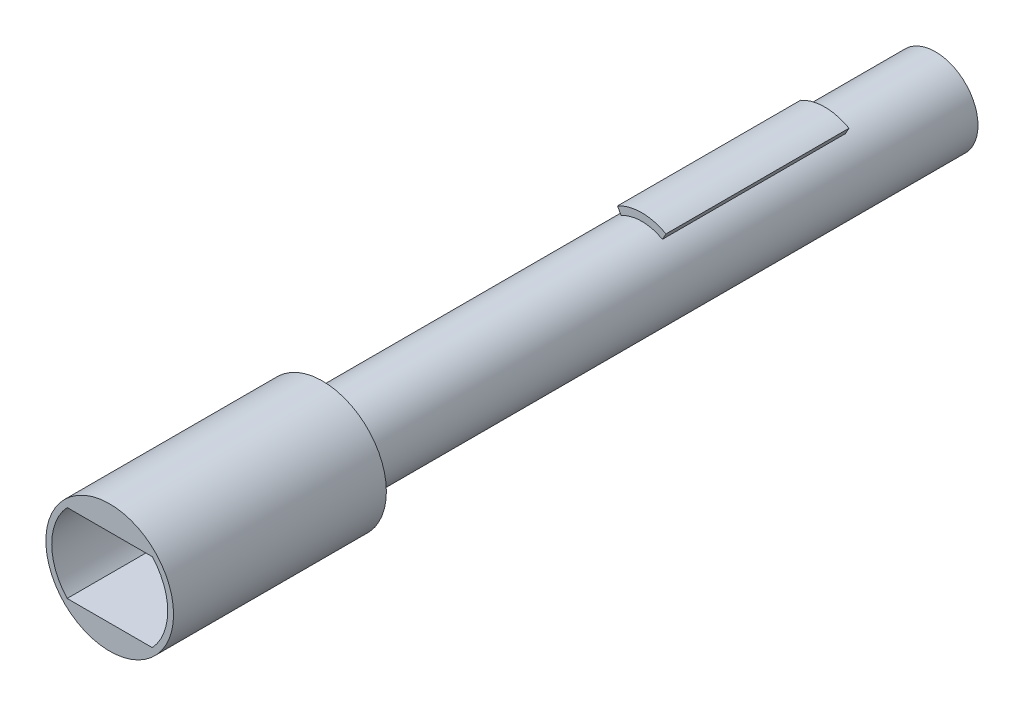
SolidWorks part; units mm, degrees
ref_plane "Front Plane" through (0, 0, 0) normal (0, 0, 1) x (1, 0, 0)
ref_plane "Top Plane" through (0, 0, 0) normal (0, 1, 0) x (1, 0, 0)
ref_plane "Right Plane" through (0, 0, 0) normal (1, 0, 0) x (0, 0, -1)
sketch "Sketch3" plane through (0, 0, 0) normal (0, 0, 1) x (1, 0, 0)
  circle A0 centre (0, 0) radius 2
  dimension "D1" = 4
extrude "Boss-Extrude1" add sketch "Sketch3" along normal blind 5.2
sketch "Sketch4" plane through (0, 0, 5.2) normal (0, 0, 1) x (1, 0, 0)
  line L0 (0, 0) -> (-1.1393, 2.0554)
  line L1 (0, 0) -> (0, 2.35)
  line L2 (0, 0) -> (1.1393, 2.0554)
  arc A0 (1.1393, 2.0554) -> (-1.1393, 2.0554) centre (0, 0) ccw
  circle A2 centre (0, 0) radius 2
  circle M5 centre (0, 0) radius 2
  dimension "D1" = 2.35
  dimension "D2" = 29
extrude "Boss-Extrude2" add sketch "Sketch4" along normal blind 8.6 contours L2 A0 L0 M5 | L0 L2 M5 | L2 L0 M5
sketch "Sketch5" plane through (0, 0, 13.8) normal (0, 0, 1) x (1, 0, 0)
  circle A0 centre (0, 0) radius 2
extrude "Boss-Extrude3" add sketch "Sketch5" along normal blind 15
sketch "Sketch6" plane through (0, 0, 28.8) normal (0, 0, 1) x (1, 0, 0)
  line L0 (0, 0) -> (2, 0) construction
  line L1 (0, 0) -> (0, 3) construction
  circle A0 centre (0, 0) radius 3
  circle A1 centre (0, 0) radius 2 construction
  dimension "D1" = 6
extrude "Boss-Extrude4" add sketch "Sketch6" along normal blind 10
sketch "Sketch7" plane through (0, 0, 38.8) normal (0, 0, 1) x (1, 0, 0)
  line L0 (0, -1.85) -> (0, 1.85) construction
  line L1 (0, 0) -> (2.725, 0) construction
  line L2 (2.0008, 1.85) -> (-2.0008, 1.85)
  line L3 (2.0008, -1.85) -> (-2.0008, -1.85)
  arc A0 (-2.0008, 1.85) -> (-2.0008, -1.85) centre (0, 0) ccw
  arc A1 (2.0008, -1.85) -> (2.0008, 1.85) centre (0, 0) ccw
  dimension "D1" = 5.45
  dimension "D2" = 1.85
extrude "Cut-Extrude1" cut sketch "Sketch7" against normal blind 8
